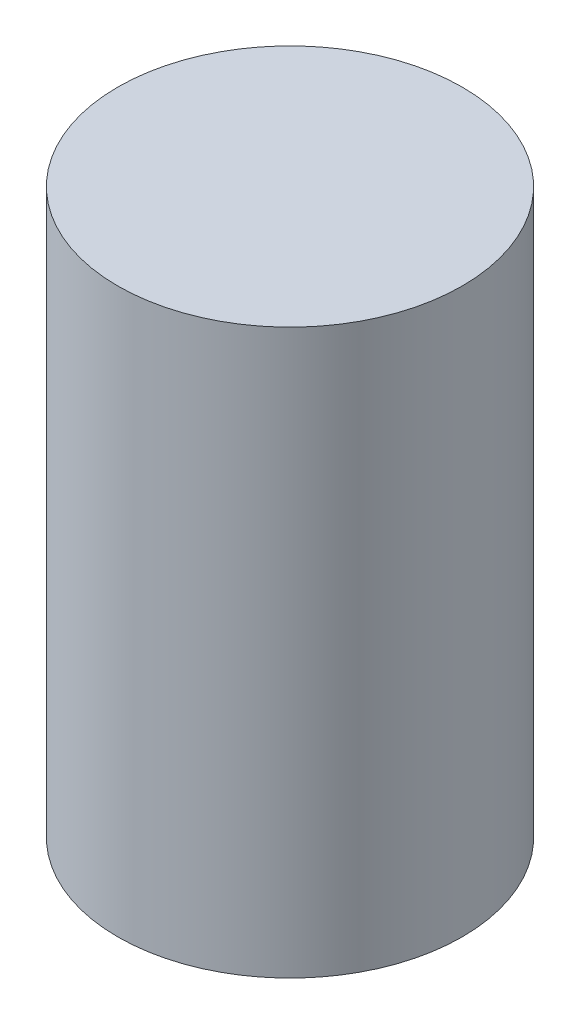
SolidWorks part; units mm, degrees
ref_plane "Front Plane" through (0, 0, 0) normal (0, 0, 1) x (1, 0, 0)
ref_plane "Top Plane" through (0, 0, 0) normal (0, 1, 0) x (1, 0, 0)
ref_plane "Right Plane" through (0, 0, 0) normal (1, 0, 0) x (0, 0, -1)
sketch "Sketch1" plane through (0, 0, 0) normal (0, 1, 0) x (1, 0, 0)
  circle A0 centre (0, 0) radius 5.5
  dimension "D1" = 11
extrude "Boss-Extrude1" add sketch "Sketch1" along normal blind 18
